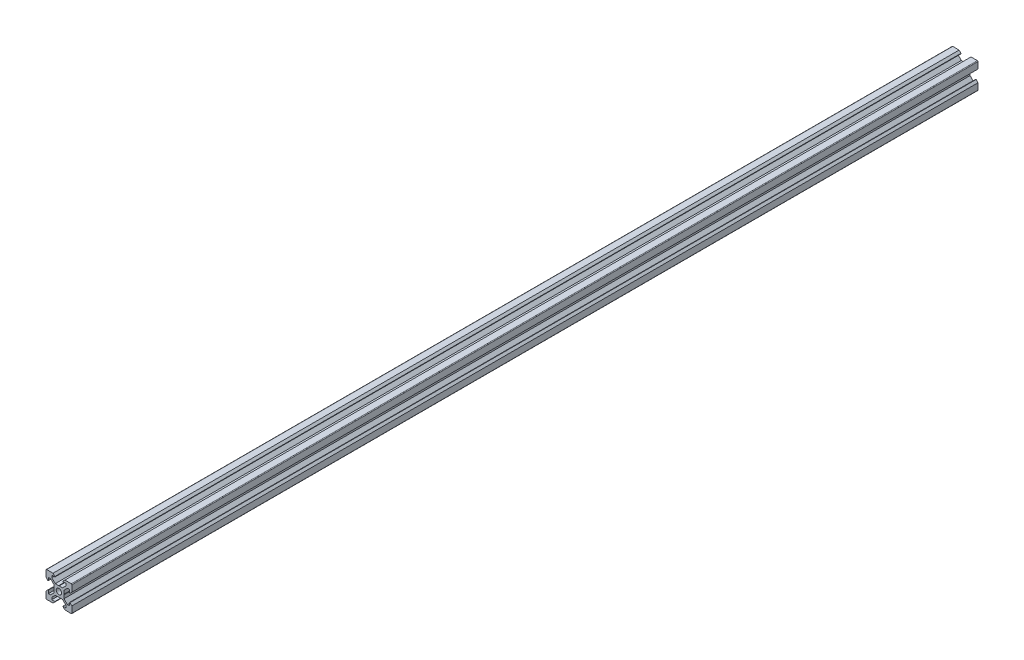
SolidWorks part; units mm, degrees
material "6061-T6 (SS)"
ref_plane "Front Plane" through (0, 0, 0) normal (0, 0, 1) x (1, 0, 0)
ref_plane "Top Plane" through (0, 0, 0) normal (0, 1, 0) x (1, 0, 0)
ref_plane "Right Plane" through (0, 0, 0) normal (1, 0, 0) x (0, 0, -1)
sketch "Sketch1" plane through (0, 0, 0) normal (0, 0, 1) x (1, 0, 0)
  line L1 (9.5, -10) -> (-9.5, -10)
  line L2 (10, -9.5) -> (10, 9.5)
  line L3 (9.5, 10) -> (-9.5, 10)
  line L4 (-10, -9.5) -> (-10, 9.5)
  line L5 (10, -10) -> (-10, 10) construction
  line L6 (10, 10) -> (-10, -10) construction
  circle A0 centre (0, 0) radius 2.1
  arc A1 (-9.5, 10) -> (-10, 9.5) centre (-9.5, 9.5) ccw
  arc A2 (10, 9.5) -> (9.5, 10) centre (9.5, 9.5) ccw
  arc A3 (9.5, -10) -> (10, -9.5) centre (9.5, -9.5) ccw
  arc A4 (-9.5, -10) -> (-10, -9.5) centre (-9.5, -9.5) cw
  point P0 (0, 0)
  line B0 (0, 0) -> (0, 10) construction
  line B1 (0, 3.69) -> (-0.21, 3.9)
  line B2 (-0.21, 3.9) -> (-2.8393, 3.9)
  line B3 (-2.8393, 3.9) -> (-5.5, 6.5607)
  line B4 (-5.5, 6.5607) -> (-5.5, 8.2)
  line B5 (-5.5, 8.2) -> (-3.125, 8.2)
  line B6 (-3.125, 8.2) -> (-3.125, 8.545)
  line B7 (-3.125, 8.545) -> (-4.58, 10)
  line B8 (-4.58, 10) -> (4.58, 10)
  line B9 (0, 0) -> (-5.9132, 5.9132) construction
  line B10 (3.125, 8.545) -> (4.58, 10)
  line B11 (3.125, 8.2) -> (3.125, 8.545)
  line B12 (5.5, 8.2) -> (3.125, 8.2)
  line B13 (5.5, 6.5607) -> (5.5, 8.2)
  line B14 (2.8393, 3.9) -> (5.5, 6.5607)
  line B15 (0.21, 3.9) -> (2.8393, 3.9)
  line B16 (0, 3.69) -> (0.21, 3.9)
  line B17 (0, 0) -> (-10, 0) construction
  line B18 (-3.69, 0) -> (-3.9, -0.21)
  line B19 (-3.9, -0.21) -> (-3.9, -2.8393)
  line B20 (-3.9, -2.8393) -> (-6.5607, -5.5)
  line B21 (-6.5607, -5.5) -> (-8.2, -5.5)
  line B22 (-8.2, -5.5) -> (-8.2, -3.125)
  line B23 (-8.2, -3.125) -> (-8.545, -3.125)
  line B24 (-8.545, -3.125) -> (-10, -4.58)
  line B25 (-10, -4.58) -> (-10, 4.58)
  line B26 (0, 0) -> (-5.9132, -5.9132) construction
  line B27 (-8.545, 3.125) -> (-10, 4.58)
  line B28 (-8.2, 3.125) -> (-8.545, 3.125)
  line B29 (-8.2, 5.5) -> (-8.2, 3.125)
  line B30 (-6.5607, 5.5) -> (-8.2, 5.5)
  line B31 (-3.9, 2.8393) -> (-6.5607, 5.5)
  line B32 (-3.9, 0.21) -> (-3.9, 2.8393)
  line B33 (-3.69, 0) -> (-3.9, 0.21)
  line B34 (0, 0) -> (0, -10) construction
  line B35 (0, -3.69) -> (0.21, -3.9)
  line B36 (0.21, -3.9) -> (2.8393, -3.9)
  line B37 (2.8393, -3.9) -> (5.5, -6.5607)
  line B38 (5.5, -6.5607) -> (5.5, -8.2)
  line B39 (5.5, -8.2) -> (3.125, -8.2)
  line B40 (3.125, -8.2) -> (3.125, -8.545)
  line B41 (3.125, -8.545) -> (4.58, -10)
  line B42 (4.58, -10) -> (-4.58, -10)
  line B43 (0, 0) -> (5.9132, -5.9132) construction
  line B44 (-3.125, -8.545) -> (-4.58, -10)
  line B45 (-3.125, -8.2) -> (-3.125, -8.545)
  line B46 (-5.5, -8.2) -> (-3.125, -8.2)
  line B47 (-5.5, -6.5607) -> (-5.5, -8.2)
  line B48 (-2.8393, -3.9) -> (-5.5, -6.5607)
  line B49 (-0.21, -3.9) -> (-2.8393, -3.9)
  line B50 (0, -3.69) -> (-0.21, -3.9)
  line B51 (0, 0) -> (10, 0) construction
  line B52 (3.69, 0) -> (3.9, 0.21)
  line B53 (3.9, 0.21) -> (3.9, 2.8393)
  line B54 (3.9, 2.8393) -> (6.5607, 5.5)
  line B55 (6.5607, 5.5) -> (8.2, 5.5)
  line B56 (8.2, 5.5) -> (8.2, 3.125)
  line B57 (8.2, 3.125) -> (8.545, 3.125)
  line B58 (8.545, 3.125) -> (10, 4.58)
  line B59 (10, 4.58) -> (10, -4.58)
  line B60 (0, 0) -> (5.9132, 5.9132) construction
  line B61 (8.545, -3.125) -> (10, -4.58)
  line B62 (8.2, -3.125) -> (8.545, -3.125)
  line B63 (8.2, -5.5) -> (8.2, -3.125)
  line B64 (6.5607, -5.5) -> (8.2, -5.5)
  line B65 (3.9, -2.8393) -> (6.5607, -5.5)
  line B66 (3.9, -0.21) -> (3.9, -2.8393)
  line B67 (3.69, 0) -> (3.9, -0.21)
  dimension "D1" = 4.2
  dimension "D3" = 0.5
  dimension "D2" = 20
sketch_block_instance "V Slot 1-4"
sketch_block "V Slot 1" parameters "D1"=10, "D2"=11, "D3"=4.3, "D4"=1.8, "D5"=0.21, "D6"=45, "D7"=9.16, "D8"=1.5, "D9"=6.25
sketch_block_instance "V Slot 1-5"
sketch_block_instance "V Slot 1-6"
sketch_block_instance "V Slot 1-7"
extrude "Boss-Extrude1" add sketch "Sketch1" along normal blind 700 contours B67 B52 B53 B54 B55 B56 B57 B58 L2 A2 L3 B10 B11 B12 B13 B14 B15 B16 B1 B2 B3 B4 B5 B6 B7 A1 L4 B27 B28 B29 B30 B31 B32 B33 B18 B19 B20 B21 B22 B23 B24 A4 L1 B44 B45 B46 B47 B48 B49
